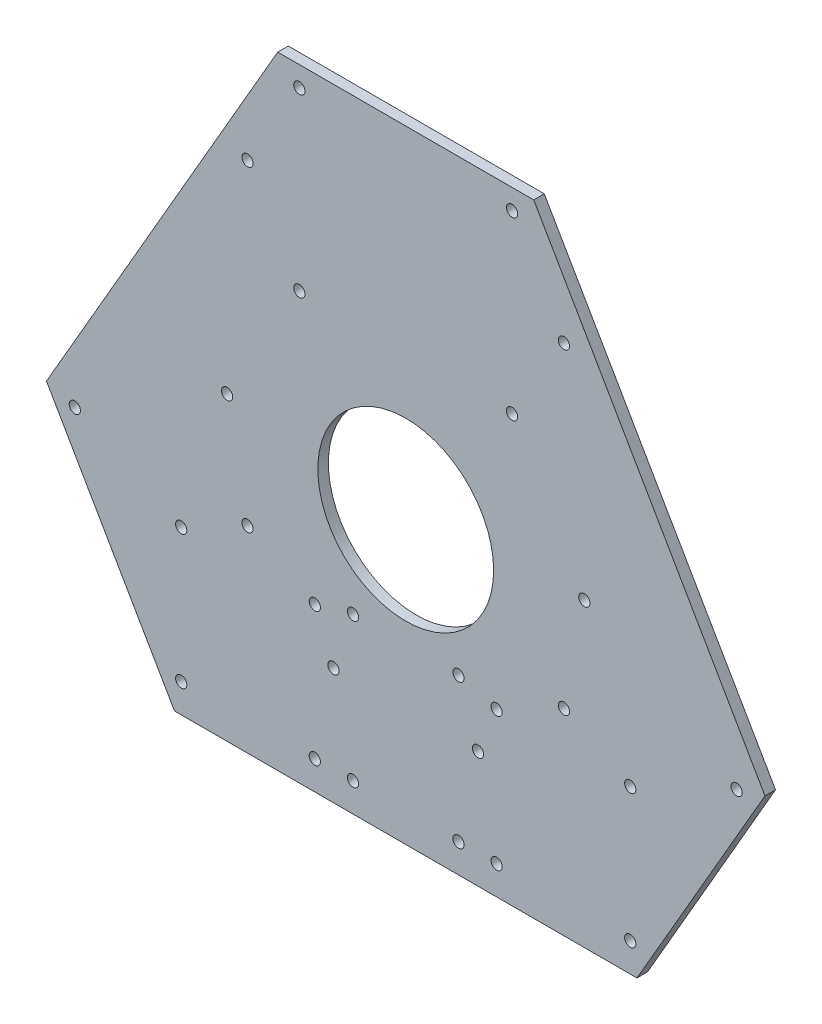
SolidWorks part; units mm, degrees
material "ｱｸﾘﾙ (中-上級の耐衝撃性)"
ref_plane "正面" through (0, 0, 0) normal (0, 0, 1) x (1, 0, 0)
ref_plane "平面" through (0, 0, 0) normal (0, 1, 0) x (1, 0, 0)
ref_plane "右側面" through (0, 0, 0) normal (1, 0, 0) x (0, 0, -1)
sketch "ｽｹｯﾁ1" plane through (0, 0, 0) normal (0, 0, 1) x (1, 0, 0)
  line L0 (0, -55) -> (0, 55) construction
  line L30 (-36.3988, 96.9554) -> (36.3988, 96.9554)
  line L31 (0, 160) -> (-138.5641, -80) construction
  line L32 (-138.5641, -80) -> (138.5641, -80) construction
  line L33 (138.5641, -80) -> (0, 160) construction
  line L34 (36.3988, 96.9554) -> (102.1653, -16.9554)
  line L35 (102.1653, -16.9554) -> (65.7665, -80)
  line L36 (65.7665, -80) -> (-65.7665, -80)
  line L37 (-65.7665, -80) -> (-102.1653, -16.9554)
  line L38 (-102.1653, -16.9554) -> (-36.3988, 96.9554)
  circle A0 centre (30.25, 91.1955) radius 1.6
  circle A1 centre (30.25, 41.1955) radius 1.6
  circle A2 centre (-30.25, 41.1955) radius 1.6
  circle A3 centre (-30.25, 91.1955) radius 1.6
  circle A4 centre (63.8526, -71.795) radius 1.6
  circle A5 centre (94.1026, -19.4005) radius 1.6
  circle A6 centre (50.8013, 5.5995) radius 1.6
  circle A7 centre (20.5513, -46.795) radius 1.6
  circle A8 centre (-94.1026, -19.4005) radius 1.6
  circle A9 centre (-63.8526, -71.795) radius 1.6
  circle A10 centre (-20.5513, -46.795) radius 1.6
  circle A11 centre (-50.8013, 5.5995) radius 1.6
  circle A12 centre (0, 0) radius 80 construction
  circle A17 centre (0, 0) radius 25
  point P0 (0, 60)
  point P46 (0, 0)
  point P48 (0, -80)
  point P76 (0, 0)
  dimension "D1" = 3.2
  dimension "D17" = 50
  dimension "D4" = 50
  dimension "D9" = 80
  dimension "D7" = 3
extrude "ﾎﾞｽ - 押し出し1" add sketch "ｽｹｯﾁ1" along normal blind 3
sketch "ｽｹｯﾁ2" plane through (0, 0, 0) normal (0, 0, -1) x (-1, 0, 0)
  line L0 (0, 1.65) -> (0, -1.65) construction
  line L1 (-45, -24) -> (45, -24) construction
  line L2 (-45, -24) -> (-45, 66) construction
  line L3 (-45, 66) -> (45, 66) construction
  line L4 (45, -24) -> (45, 66) construction
  line L5 (-45, -24) -> (45, 66) construction
  line L6 (-45, 66) -> (45, -24) construction
  line L7 (-15, -30.795) -> (15, -30.795) construction
  line L8 (-15, -30.795) -> (-15, -71.795) construction
  line L9 (-15, -71.795) -> (15, -71.795) construction
  line L10 (15, -30.795) -> (15, -71.795) construction
  line L11 (-15, -30.795) -> (15, -71.795) construction
  line L12 (-15, -71.795) -> (15, -30.795) construction
  line L13 (-63.8526, -33.795) -> (-25.8526, -33.795) construction
  line L14 (-63.8526, -33.795) -> (-63.8526, -71.795) construction
  line L15 (-63.8526, -71.795) -> (-25.8526, -71.795) construction
  line L16 (-25.8526, -33.795) -> (-25.8526, -71.795) construction
  line L17 (-63.8526, -33.795) -> (-25.8526, -71.795) construction
  line L18 (-63.8526, -71.795) -> (-25.8526, -33.795) construction
  line L25 (0, 96.9554) -> (0, -80) construction
  line L26 (36.3988, 96.9554) -> (-36.3988, 96.9554) construction
  line L27 (-65.7665, -80) -> (65.7665, -80) construction
  line L28 (63.8526, -71.795) -> (25.8526, -33.795) construction
  line L29 (63.8526, -33.795) -> (25.8526, -71.795) construction
  line L30 (25.8526, -33.795) -> (25.8526, -71.795) construction
  line L31 (63.8526, -71.795) -> (25.8526, -71.795) construction
  line L32 (63.8526, -33.795) -> (63.8526, -71.795) construction
  line L33 (63.8526, -33.795) -> (25.8526, -33.795) construction
  circle A0 centre (-63.8526, -33.795) radius 1.6
  circle A1 centre (-25.8526, -33.795) radius 1.6
  circle A2 centre (-25.8526, -71.795) radius 1.6
  circle A3 centre (-63.8526, -71.795) radius 1.6
  circle A4 centre (15, -30.795) radius 1.6
  circle A5 centre (-15, -30.795) radius 1.6
  circle A6 centre (-15, -71.795) radius 1.6
  circle A7 centre (15, -71.795) radius 1.6
  circle A8 centre (45, 66) radius 1.6
  circle A9 centre (-45, 66) radius 1.6
  circle A10 centre (-45, -24) radius 1.6
  circle A11 centre (45, -24) radius 1.6
  circle A16 centre (-63.8526, -71.795) radius 1.6 construction
  circle A17 centre (63.8526, -71.795) radius 1.6
  circle A18 centre (25.8526, -71.795) radius 1.6
  circle A19 centre (25.8526, -33.795) radius 1.6
  circle A20 centre (63.8526, -33.795) radius 1.6
  point P0 (0, 21)
  point P5 (0, -51.295)
  point P10 (-44.8526, -52.795)
  point P46 (44.8526, -52.795)
  dimension "D1" = 3.2
  dimension "D2" = 90
  dimension "D3" = 90
  dimension "D4" = 38
  dimension "D5" = 30
  dimension "D6" = 41
  dimension "D7" = 56
extrude "ｶｯﾄ - 押し出し1" cut sketch "ｽｹｯﾁ2" against normal through all
